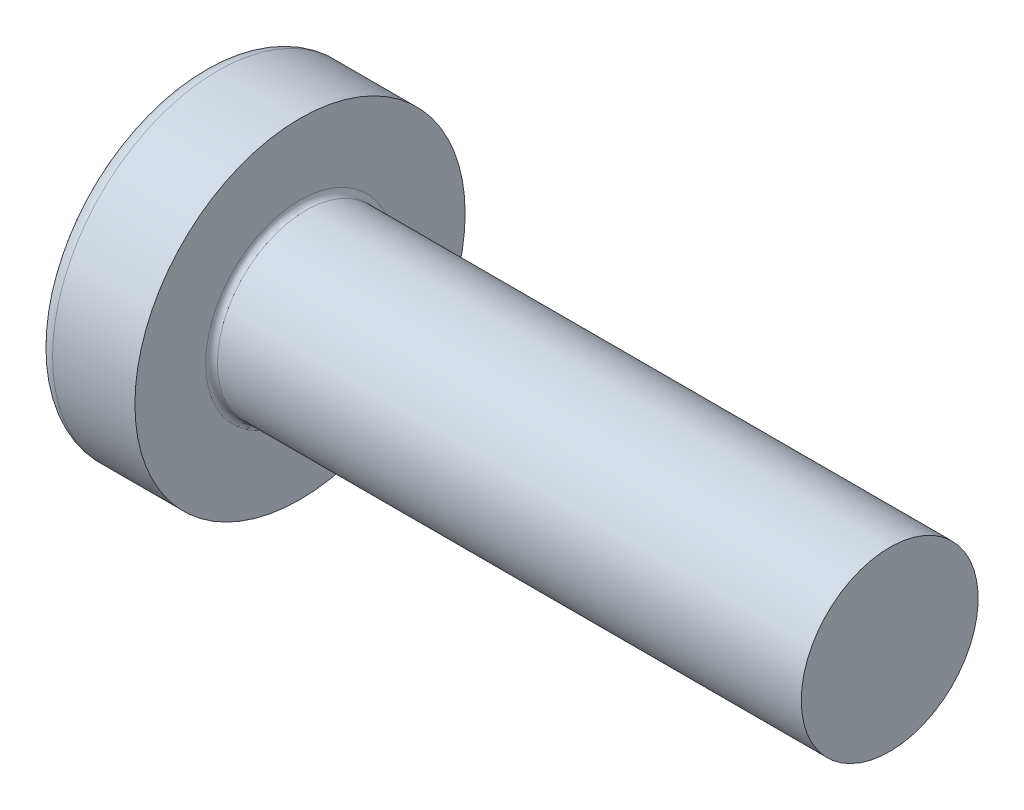
SolidWorks part; units mm, degrees
ref_plane "Plane1" through (0, 0, 0) normal (0, 0, 1) x (1, 0, 0)
ref_plane "Plane2" through (0, 0, 0) normal (0, 1, 0) x (1, 0, 0)
ref_plane "Plane3" through (0, 0, 0) normal (1, 0, 0) x (0, 0, -1)
sketch "BodySke" plane through (0, 0, 0) normal (0, 0, 1) x (1, 0, 0)
  line L0 (2.4, 1.5) -> (2.4, 2.8)
  line L1 (2.65, 6.35) -> (2.65, -3.175) construction
  line L2 (-25.4, 0) -> (127, 0) construction
  line L3 (12.4, 0) -> (0, 0)
  line L4 (2.4, 1.5) -> (12.4, 1.5)
  line L5 (12.4, 1.5) -> (12.4, 0)
  line L6 (1.0035, 2.8) -> (2.4, 2.8)
  line L8 (2.4, 6.35) -> (2.4, -3.175) construction
  arc A0 (0.7754, 2.6744) -> (0, 0) centre (5, 0) ccw
  arc A2 (0.7754, 2.6744) -> (1.0035, 2.8) centre (1.0035, 2.53) cw
  dimension "Head_crown_rad" = 5
  dimension "Head_fillet_rad" = 0.27
  dimension "Head_ht" = 2.4
  dimension "Head_dia" = 5.6
  dimension "Advance" = 0.5
  dimension "Diameter" = 3
revolve "Base-Revolve" add sketch "BodySke"
cosmetic thread "ThreadCosmetic" [suppressed]
fillet "Fillet1" radius 0.1 1 edges at (2.4, 0, 1.5)
sketch "Sketch3" plane through (0, 0, 0) normal (1, 0, 0) x (0, 0, -1)
  line L0 (0.37, -1.4) -> (-0.37, -1.4)
  line L1 (0.37, -1.4) -> (0.37, 1.4)
  line L2 (-0.37, 1.4) -> (0.37, 1.4)
  line L3 (-0.37, 1.4) -> (-0.37, -1.4)
  dimension "Cross_dia" = 2.8
  dimension "D1" = 1.4
  dimension "Cross_width" = 0.74
  dimension "D2" = 0.37
ref_plane "Plane4" through (1.75, 0, 0) normal (1, 0, 0) x (0, 0, -1)
sketch "Sketch4" plane through (1.75, 0, 0) normal (1, 0, 0) x (0, 0, -1)
  line L0 (0.37, -0.5275) -> (-0.37, -0.5275)
  line L1 (0.37, -0.5275) -> (0.37, 0.5275)
  line L2 (-0.37, 0.5275) -> (0.37, 0.5275)
  line L3 (-0.37, 0.5275) -> (-0.37, -0.5275)
  dimension "D1" = 0.74
  dimension "D2" = 1.055
  dimension "D3" = 0.37
  dimension "D4" = 0.5275
loft "Recess" cut profiles "Sketch3", "Sketch4"
pattern_circular "RecPat" count 2 every 90 about axis through (0, 0, 0) along (1, 0, 0) of "Recess"
sketch "RecCorSke" plane through (0, 0, 0) normal (0, 0, 1) x (1, 0, 0)
  line L0 (-3.175, 0) -> (15.875, 0) construction
  line L1 (-25.4, 0) -> (127, 0) construction
  line L2 (0, 0) -> (0, 0.6784)
  line L3 (0, 0.6784) -> (1.75, 0.556)
  line L4 (1.75, 0.556) -> (1.9307, 0)
  line L5 (1.9307, 0) -> (0, 0)
  dimension "Diameter" = 1.112
  dimension "Depth" = 1.75
  dimension "Draft_angle" = 4
  dimension "Bottom_angle" = 18
revolve "RecessCore" cut sketch "RecCorSke" angle 360 about L0
sketch "ThdSchSke" plane through (0, 0, 0) normal (0, 0, 1) x (1, 0, 0)
  line L0 (3.4, -1.2195) -> (3.2036, -1.5)
  line L1 (3.4, -1.2195) -> (3.5964, -1.5)
  line L2 (3.5964, -1.5) -> (3.5964, -1.875)
  line L3 (-3.175, 0) -> (5.1513, 0) construction
  line L5 (3.5964, -1.875) -> (3.2036, -1.875)
  line L6 (3.2036, -1.875) -> (3.2036, -1.5)
  dimension "Diameter" = 3
  dimension "SideAngle" = 55
  dimension "VeeAngle" = 70
  dimension "Thread_minor" = 2.439
  dimension "Overcut" = 3.75
  dimension "Start" = 3.4
revolve "ThreadSchematic" [suppressed] cut sketch "ThdSchSke" angle 360 about L3
pattern_linear "ThdSchPat" [suppressed]
equation "\"D1@Sketch3\" = \"Cross_dia@Sketch3\" / 2"
equation "\"D2@Sketch3\" = \"Cross_width@Sketch3\" / 2"
equation "\"Depth@RecCorSke\" = \"Cross_depth@Plane4\""
equation "\"D1@Sketch4\" = \"Cross_width@Sketch3\""
equation "\"D2@Sketch4\" = \"Cross_dia@Sketch3\" - 2.0 * \"Cross_depth@Plane4\" * tan(26.5  * 0.017453292)"
equation "\"D3@Sketch4\" = \"D1@Sketch4\" / 2"
equation "\"D4@Sketch4\" = \"D2@Sketch4\" / 2"
equation "\"Thread_length@ThreadCosmetic\" = ((sgn( (\"Length@BodySke\" - \"Advance@BodySke\" * 2.0 ) - \"Thread_nom@BodySke\" )-1)*( (\"Length@BodySke\" - \"Advance@BodySke\" * 2.0 ) - \"Thread_nom@BodySke\" ))/-2+ \"Thread_nom@BodySke\""
equation "\"Thread_minor@ThdSchSke\" = \"Thread_minor@ThreadCosmetic\""
equation "\"Diameter@ThdSchSke\" = \"Diameter@BodySke\""
equation "\"Overcut@ThdSchSke\" = \"Diameter@BodySke\" * 1.25"
equation "\"Start@ThdSchSke\" = \"Head_ht@BodySke\" + \"Length@BodySke\" - \"Thread_length@ThreadCosmetic\"  '---Non-countersunk---"
equation "\"Num_threads@ThdSchPat\" = int( \"Thread_length@ThreadCosmetic\" / \"Advance@BodySke\" + 0.999 )  + 1"
equation "\"Advance@ThdSchPat\" = \"Thread_length@ThreadCosmetic\" /  (\"Num_threads@ThdSchPat\" - 1) 'relax it"
